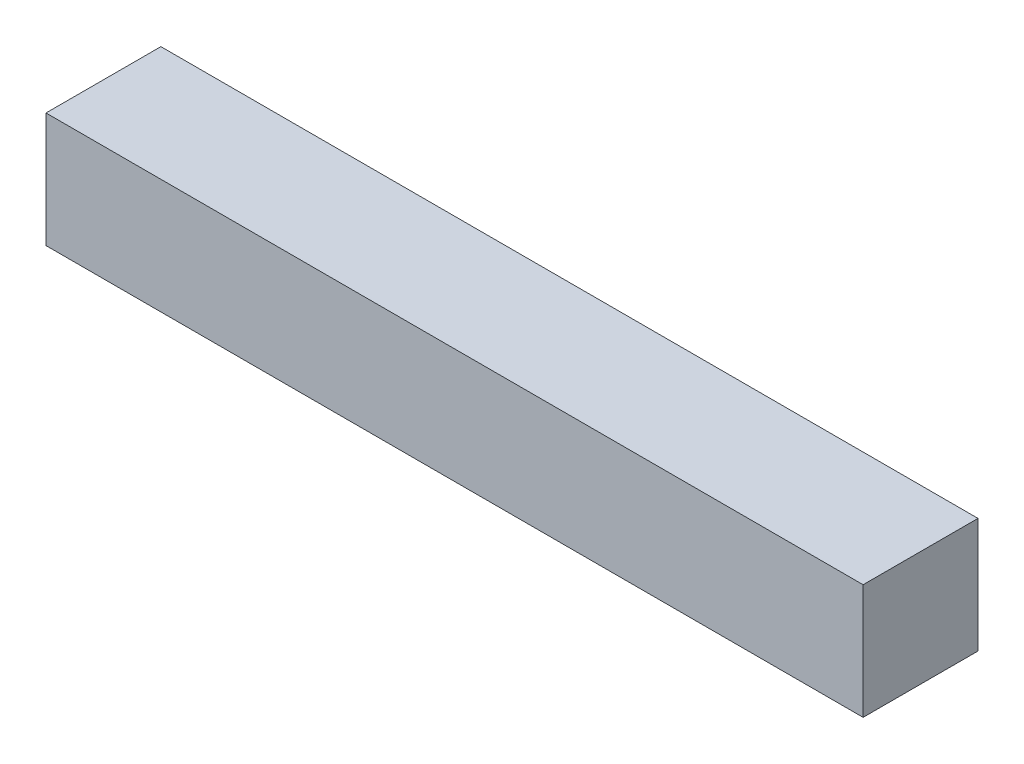
SolidWorks part; units mm, degrees
ref_plane "Front" through (0, 0, 0) normal (0, 0, 1) x (1, 0, 0)
ref_plane "Top" through (0, 0, 0) normal (0, 1, 0) x (1, 0, 0)
ref_plane "Right" through (0, 0, 0) normal (1, 0, 0) x (0, 0, -1)
sketch "Sketch1" plane through (0, 0, 0) normal (0, 0, 1) x (1, 0, 0)
  line L1 (-12.7, 215.5) -> (-190.5, 215.5)
  line L5 (-190.5, 215.5) -> (-190.5, 190.5)
  line L6 (-12.7, 215.5) -> (-12.7, 190.5)
  line L7 (-12.7, 190.5) -> (-190.5, 190.5)
  dimension "D1" = 25
extrude "Base-Extrude" add sketch "Sketch1" along normal blind 25
